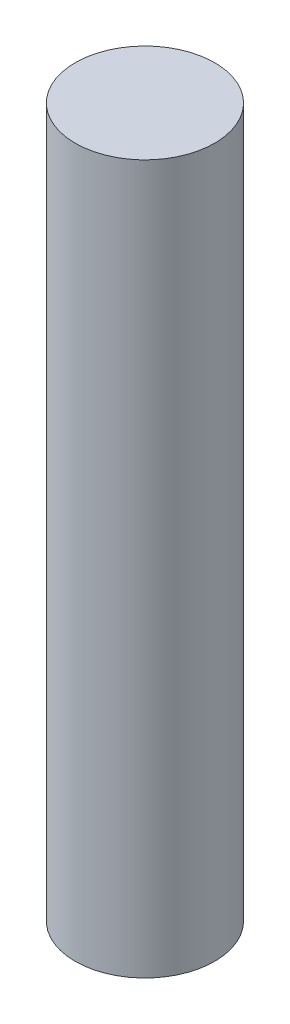
SolidWorks part; units mm, degrees
ref_plane "Front Plane" through (0, 0, 0) normal (0, 0, 1) x (1, 0, 0)
ref_plane "Top Plane" through (0, 0, 0) normal (0, 1, 0) x (1, 0, 0)
ref_plane "Right Plane" through (0, 0, 0) normal (1, 0, 0) x (0, 0, -1)
sketch "스케치1" plane through (0, 0, 0) normal (0, 1, 0) x (1, 0, 0)
  circle A0 centre (0, 0) radius 9.45
extrude "보스-돌출1" add sketch "스케치1" along normal blind 96
